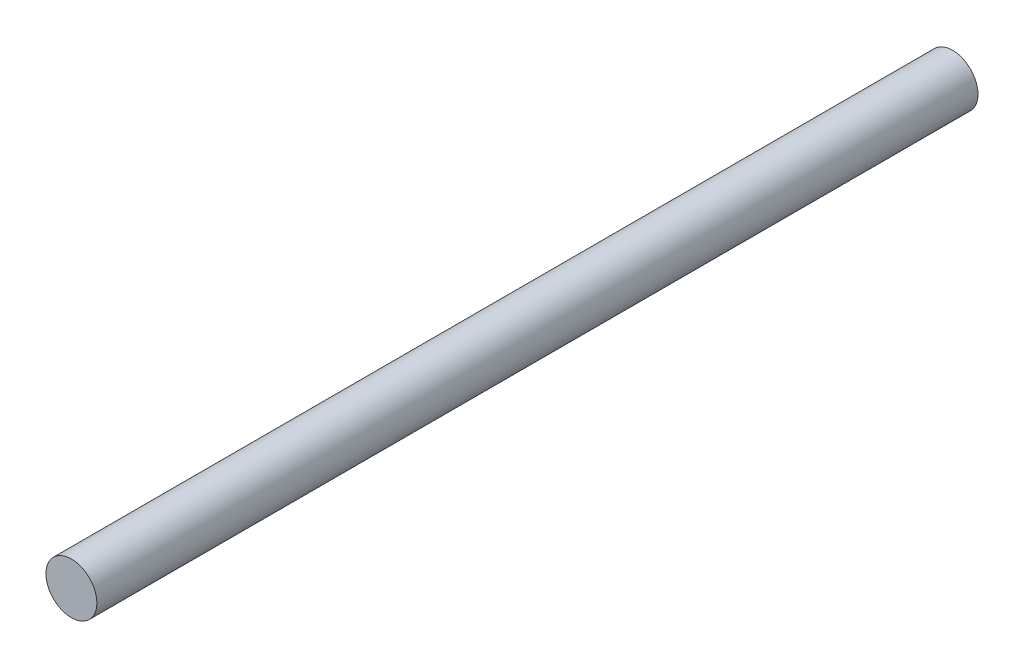
SolidWorks part; units mm, degrees
ref_plane "Front Plane" through (0, 0, 0) normal (0, 0, 1) x (1, 0, 0)
ref_plane "Top Plane" through (0, 0, 0) normal (0, 1, 0) x (1, 0, 0)
ref_plane "Right Plane" through (0, 0, 0) normal (1, 0, 0) x (0, 0, -1)
sketch "Sketch1" plane through (0, 0, 0) normal (0, 0, 1) x (1, 0, 0)
  circle A0 centre (0, 0) radius 1.3
extrude "Boss-Extrude1" add sketch "Sketch1" along normal blind 45
